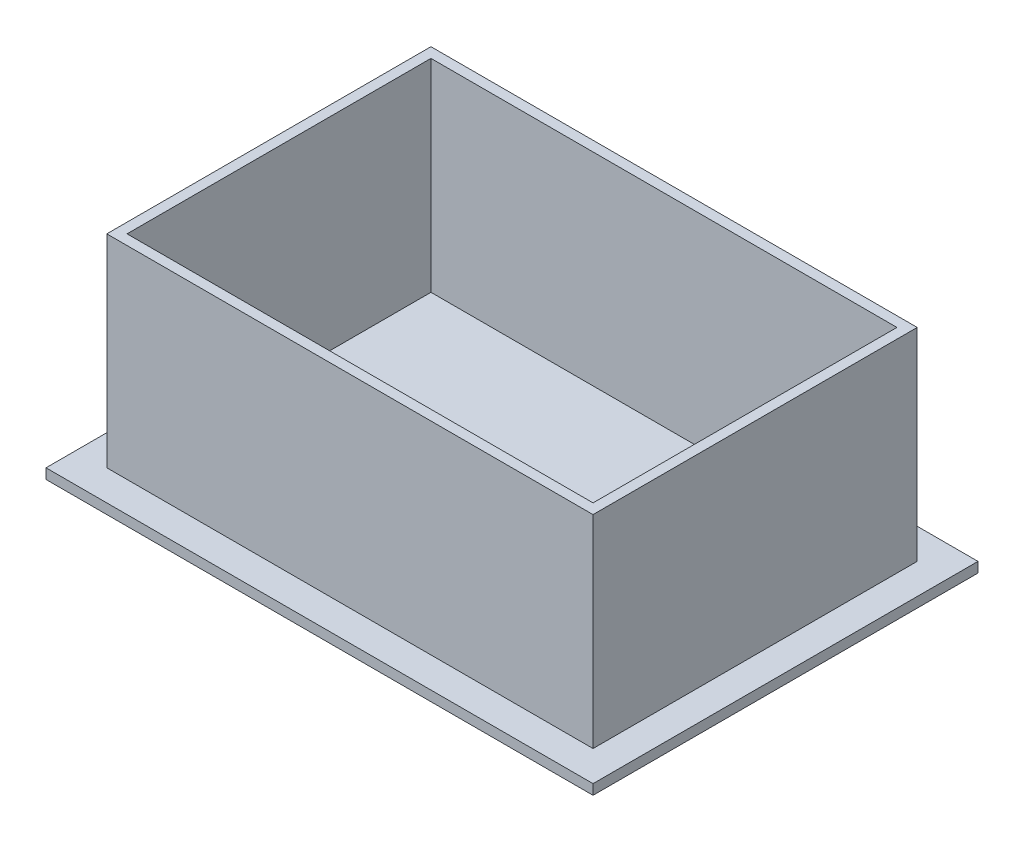
SolidWorks part; units mm, degrees
ref_plane "Front Plane" through (0, 0, 0) normal (0, 0, 1) x (1, 0, 0)
ref_plane "Top Plane" through (0, 0, 0) normal (0, 1, 0) x (1, 0, 0)
ref_plane "Right Plane" through (0, 0, 0) normal (1, 0, 0) x (0, 0, -1)
sketch "Sketch1" plane through (0, 0, 0) normal (0, 1, 0) x (1, 0, 0)
  line L1 (-85.725, -60.325) -> (85.725, -60.325)
  line L2 (-85.725, -60.325) -> (-85.725, 60.325)
  line L3 (-85.725, 60.325) -> (85.725, 60.325)
  line L4 (85.725, -60.325) -> (85.725, 60.325)
  line L5 (-85.725, -60.325) -> (85.725, 60.325) construction
  line L6 (-85.725, 60.325) -> (85.725, -60.325) construction
  point P0 (0, 0)
  dimension "D1" = 120.65
  dimension "D2" = 171.45
extrude "Boss-Extrude1" add sketch "Sketch1" along normal blind 3.175
sketch "Sketch2" plane through (0, 3.175, 0) normal (0, 1, 0) x (1, 0, 0)
  line L0 (-76.2, 50.8) -> (76.2, 50.8)
  line L1 (-73.025, -47.625) -> (73.025, -47.625)
  line L2 (-73.025, -47.625) -> (-73.025, 47.625)
  line L3 (-73.025, 47.625) -> (73.025, 47.625)
  line L4 (73.025, -47.625) -> (73.025, 47.625)
  line L5 (-73.025, -47.625) -> (73.025, 47.625) construction
  line L6 (-73.025, 47.625) -> (73.025, -47.625) construction
  line L7 (76.2, -50.8) -> (76.2, 50.8)
  line L8 (-76.2, -50.8) -> (76.2, -50.8)
  line L9 (-76.2, -50.8) -> (-76.2, 50.8)
  point P0 (0, 0)
  dimension "D1" = 146.05
  dimension "D2" = 95.25
  dimension "D3" = 3.175
extrude "Boss-Extrude2" add sketch "Sketch2" along normal blind 63.5
